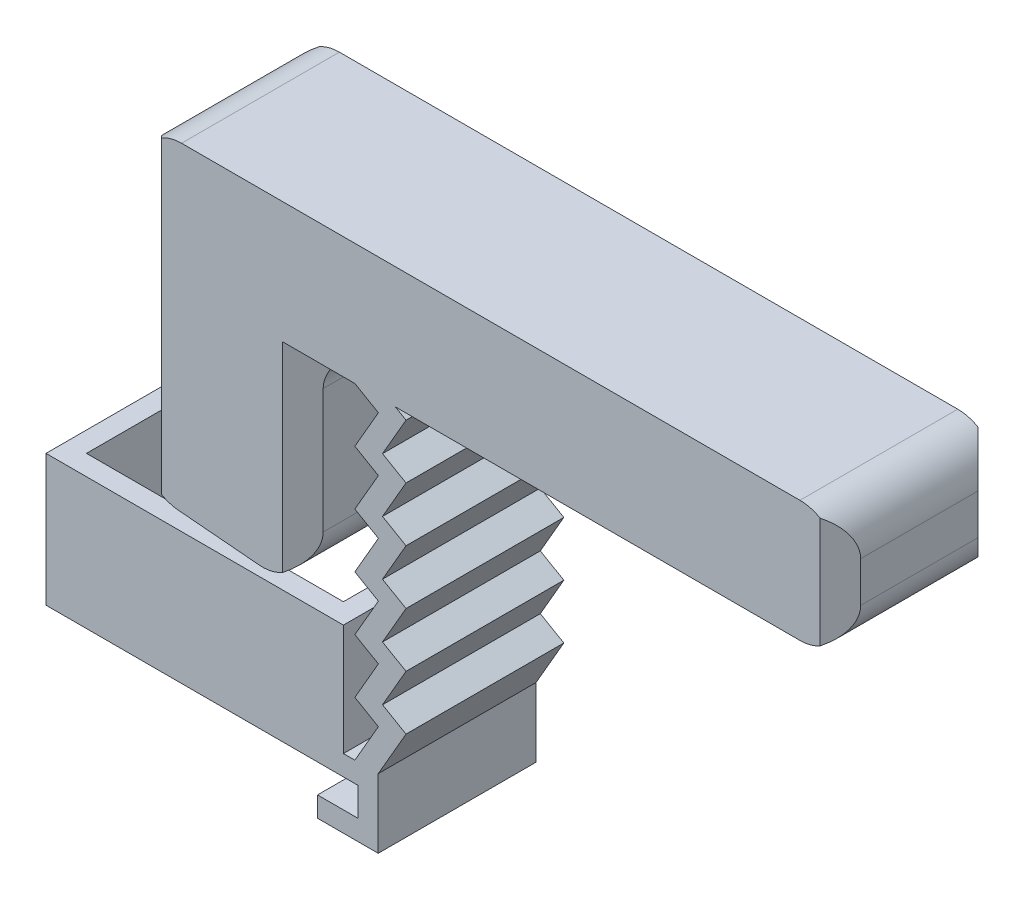
SolidWorks part; units mm, degrees
ref_plane "Front Plane" through (0, 0, 0) normal (0, 0, 1) x (1, 0, 0)
ref_plane "Top Plane" through (0, 0, 0) normal (0, 1, 0) x (1, 0, 0)
ref_plane "Right Plane" through (0, 0, 0) normal (1, 0, 0) x (0, 0, -1)
sketch "Sketch2" plane through (0, 0, 0) normal (0, 1, 0) x (1, 0, 0)
  line L0 (30.215, 56.2321) -> (30.215, 50.4321) construction
  line L1 (30.215, 50.4321) -> (17.515, 50.4321) construction
  line L2 (17.515, 50.4321) -> (17.515, 56.2321) construction
  line L3 (30.215, 56.2321) -> (30.215, 50.4321)
  line L4 (30.215, 50.4321) -> (17.515, 50.4321)
  line L5 (17.515, 50.4321) -> (17.515, 56.2321)
  line L6 (31.215, 57.2321) -> (31.215, 49.4321)
  line L7 (31.215, 49.4321) -> (16.515, 49.4321)
  line L8 (16.515, 49.4321) -> (16.515, 57.2321)
  line L12 (28.215, 57.2321) -> (31.215, 57.2321)
  line L14 (31.215, 56.2321) -> (31.215, 49.4321) construction
  line L15 (16.515, 49.4321) -> (16.515, 56.2321) construction
  line L18 (30.215, 56.2321) -> (28.215, 56.2321)
  line L19 (28.215, 56.2321) -> (28.215, 57.2321)
  line L20 (16.515, 57.2321) -> (19.515, 57.2321)
  line L21 (19.515, 57.2321) -> (19.515, 56.2321)
  line L22 (17.515, 56.2321) -> (30.215, 56.2321) construction
  line L23 (19.515, 56.2321) -> (17.515, 56.2321)
  dimension "D2" = 2
  dimension "D3" = 1
  dimension "D1" = 1
extrude "Boss-Extrude3" add sketch "Sketch2" along normal blind 6.5 contours L6 L7 L8 L20 L21 L23 L5 L4 L3 L18 L19 L12
sketch "Sketch1" plane through (-49.4321, 0, -49.4321) normal (0, 0, 1) x (1, 0, 0)
  line L27 (81.2124, 1) -> (82.3761, 3.0155)
  line L28 (82.3761, 3.0155) -> (81.2124, 3.6874)
  line L31 (79.3671, -1.41) -> (81.3671, -1.41)
  line L32 (81.3671, -1.41) -> (81.3671, 0)
  line L33 (81.3671, 0) -> (80.6471, 0)
  line L34 (81.3671, 0) -> (61.0471, 0) construction
  line L35 (81.2124, 14.437) -> (82.3761, 16.4525)
  line L36 (81.3671, -1.51) -> (81.3671, 0) construction
  line L37 (79.3671, -2.41) -> (82.3671, -2.41)
  line L38 (82.3671, -2.41) -> (82.3671, 1)
  line L39 (81.2124, 1) -> (80.6471, 1)
  line L40 (79.3671, -1.41) -> (79.3671, -2.41)
  line L41 (80.6471, 1) -> (80.6471, 0)
  line L42 (81.2124, 3.6874) -> (82.3761, 5.7029)
  line L43 (82.3761, 5.7029) -> (81.2124, 6.3748)
  line L44 (81.2124, 6.3748) -> (82.3761, 8.3903)
  line L45 (82.3761, 8.3903) -> (81.2124, 9.0622)
  line L46 (81.2124, 9.0622) -> (82.3761, 11.0777)
  line L47 (82.3761, 11.0777) -> (81.2124, 11.7496)
  line L48 (81.2124, 11.7496) -> (82.3761, 13.7651)
  line L49 (82.3761, 13.7651) -> (81.2124, 14.437)
  line L50 (82.3671, 1) -> (83.7421, 3.3816)
  line L51 (104.7846, 22.9706) -> (104.7846, 16.9706) construction
  line L52 (82.5784, 4.0534) -> (83.7421, 6.069)
  line L53 (83.7421, 6.069) -> (82.5784, 6.7408)
  line L54 (82.5784, 6.7408) -> (83.7421, 8.7564)
  line L55 (83.7421, 8.7564) -> (82.5784, 9.4282)
  line L56 (82.5784, 9.4282) -> (83.7421, 11.4437)
  line L57 (83.7421, 11.4437) -> (82.5784, 12.1156)
  line L58 (82.5784, 12.1156) -> (83.7421, 14.1311)
  line L59 (105.2124, 17.1244) -> (83.2124, 17.1244)
  line L60 (82.1277, 0.5854) -> (83.7421, 3.3816) construction
  line L61 (82.3761, 16.4525) -> (81.2124, 17.1244)
  line L62 (83.7421, 3.3816) -> (82.5784, 4.0534)
  line L63 (82.5784, 4.0534) -> (83.7421, 6.069)
  line L64 (83.7421, 14.1311) -> (81.7124, 15.303) construction
  line L65 (83.7421, 6.069) -> (82.5784, 6.7408)
  line L66 (82.5784, 6.7408) -> (83.7421, 8.7564)
  line L67 (83.7421, 8.7564) -> (82.5784, 9.4282)
  line L68 (82.5784, 9.4282) -> (83.7421, 11.4437)
  line L69 (83.7421, 11.4437) -> (82.5784, 12.1156)
  line L70 (82.5784, 12.1156) -> (83.7421, 14.1311)
  line L71 (83.7421, 14.1311) -> (82.5784, 14.803)
  line L72 (82.5784, 14.803) -> (83.7421, 16.8185)
  line L73 (83.7421, 16.8185) -> (83.2124, 17.1244)
  line L74 (83.7421, 16.8185) -> (81.7124, 17.9904) construction
  line L75 (81.2617, 1.0854) -> (82.3761, 3.0155) construction
  line L76 (82.3671, 1) -> (80.6471, 1) construction
  line L77 (82.1277, 0.5854) -> (83.7421, 3.3816) construction
  line L78 (78.6471, 17.1244) -> (78.6471, 6.8)
  line L79 (78.6471, 6.8) -> (70.6471, 7.4999)
  line L80 (70.6471, 7.4999) -> (70.6471, 23.1244)
  line L81 (70.6471, 23.1244) -> (105.2124, 23.1244)
  line L82 (105.2124, 23.1244) -> (105.2124, 17.1244)
  line L83 (81.2124, 17.1244) -> (78.6471, 17.1244)
  line L85 (82.3671, -2.41) -> (82.3671, 1) construction
  line L86 (83.7421, 3.3816) -> (82.5784, 4.0534) construction
  dimension "D3" = 0.1
  dimension "D4" = 2
  dimension "D6" = 30
  dimension "D7" = 90
  dimension "D9" = 2.75
  dimension "D11" = 85
  dimension "D12" = 1
  dimension "D13" = 8
  dimension "D14" = 0.3
  dimension "D15" = 6
  dimension "D16" = 22
  dimension "D17" = 28.1576
  dimension "D18" = 2.52
  dimension "D2" = 1
  dimension "D5" = 1
  dimension "D8" = 1
  dimension "D1" = 6
extrude "Boss-Extrude4" add sketch "Sketch1" against normal up to surface (7.8 mm away) up to face at (29.715, 3.25, -57.2321)
chamfer "Chamfer1" distance 1 angle 45 6 edges at (21.215, 15.3121, -57.2321) (21.215, 15.3121, -49.4321) (29.215, 11.9622, -57.2321) (29.215, 11.9622, -49.4321) (55.7803, 20.1244, -57.2321) (55.7803, 20.1244, -49.4321)
fillet "Fillet1" radius 2 6 edges at (29.215, 6.8, -53.3321) (29.215, 17.1244, -53.3321) (21.215, 7.4999, -53.3321) (21.215, 23.1244, -53.3321) (55.7803, 17.1244, -53.3321) (55.7803, 23.1244, -53.3321)
